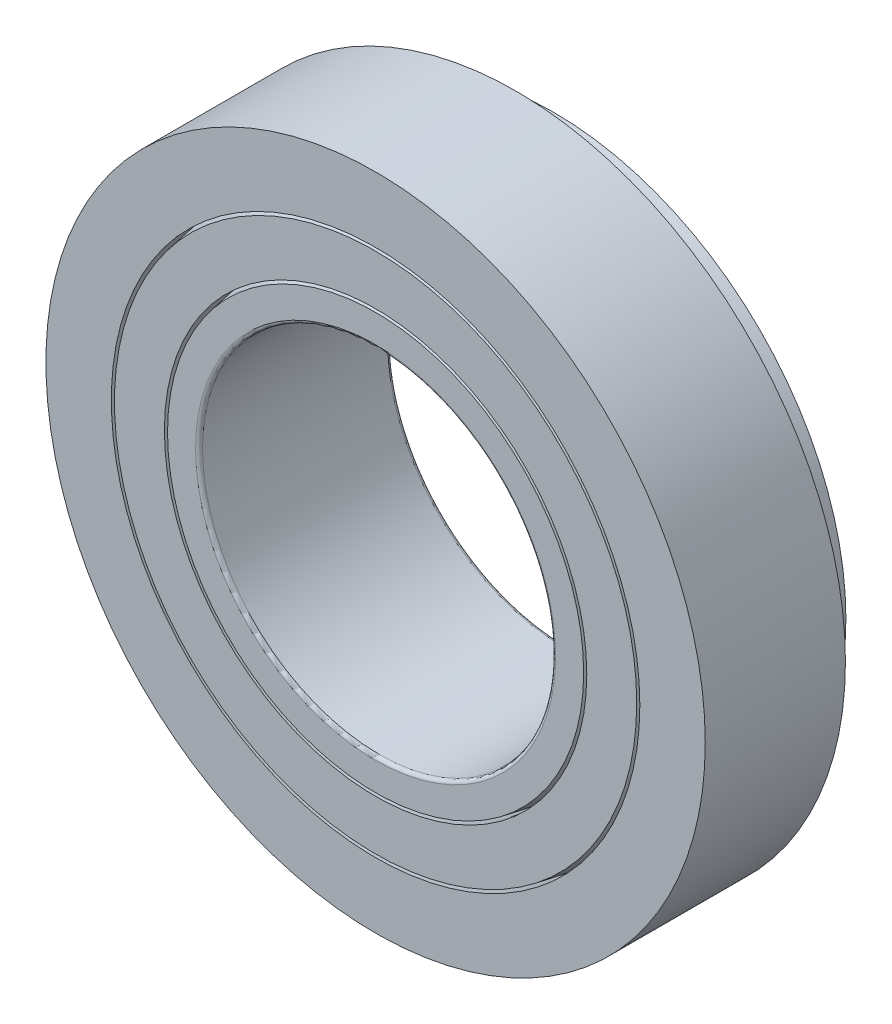
SolidWorks part; units mm, degrees
material "Alloy Steel"
ref_plane "Front Plane" through (0, 0, 0) normal (0, 0, 1) x (1, 0, 0)
ref_plane "Top Plane" through (0, 0, 0) normal (0, 1, 0) x (1, 0, 0)
ref_plane "Right Plane" through (0, 0, 0) normal (1, 0, 0) x (0, 0, -1)
sketch "Sketch1" plane through (0, 0, 0) normal (1, 0, 0) x (0, 0, -1)
  line L0 (-7.3422, 0) -> (7.3422, 0) construction
  line L1 (0, 0) -> (0, 25.2016) construction
  line L2 (-7.3422, 13.4937) -> (7.3422, 13.4937) construction
  line L3 (7.3422, 13.4937) -> (7.3422, 18.4944) construction
  line L4 (7.3422, 18.4944) -> (-7.3422, 15.9051) construction
  line L5 (-7.3422, 15.9051) -> (-7.3422, 13.4937) construction
  line L7 (-7.3422, 25.2016) -> (3.3734, 25.2016)
  line L8 (3.3734, 25.2016) -> (3.3734, 22.0904)
  line L9 (3.3734, 22.0904) -> (-7.3422, 20.2009)
  line L10 (-7.3422, 20.2009) -> (-7.3422, 25.2016)
  line L11 (-7.3422, 20.2009) -> (-6.6076, 16.0347) construction
  line L12 (6.2107, 22.5907) -> (6.9453, 18.4244) construction
  line L14 (-7.3422, 15.9051) -> (-6.6076, 16.0347) construction
  line L15 (-7.3422, 15.9051) -> (6.9453, 18.4244) construction
  point P5 (0, 13.4937)
  dimension "D1" = 100
  dimension "Width" = 14.6844
  dimension "OD" = 50.4031
  dimension "Shaft Dia" = 26.9875
  dimension "D2" = 11.7078
  dimension "D3" = 5.0006
  dimension "Outer Wd" = 10.7156
  dimension "Bearing Wd" = 14.2875
revolve "Revolve1" add sketch "Sketch1" angle 360 about L0
sketch "Sketch5" plane through (0, 0, 0) normal (1, 0, 0) x (0, 0, -1)
  line L0 (7.3422, 18.4944) -> (-7.3422, 15.9051) construction
  line L1 (7.3422, 18.4944) -> (-7.3422, 15.9051)
  line L2 (-7.3422, 15.9051) -> (-7.3422, 13.4937)
  line L3 (-7.3422, 13.4937) -> (7.3422, 13.4937)
  line L4 (7.3422, 13.4937) -> (7.3422, 18.4944)
revolve "Revolve4" add sketch "Sketch5" angle 360 about L0
sketch "Sketch2" plane through (0, 0, 0) normal (1, 0, 0) x (0, 0, -1)
  line L0 (-7.3422, 19.9616) -> (-7.3422, 16.1444)
  line L1 (3.3734, 21.8511) -> (6.2516, 22.3586)
  line L2 (-7.3422, 16.1444) -> (3.3734, 18.0339)
  line L3 (6.2107, 22.5907) -> (6.9453, 18.4244) construction
  line L4 (3.3734, 18.0339) -> (3.3734, 21.8511) construction
  line L5 (3.3734, 21.8511) -> (-7.3422, 19.9616)
  line L6 (3.3734, 22.0904) -> (-7.3422, 20.2009) construction
  line L7 (7.3422, 18.4944) -> (-7.3422, 15.9051) construction
  line L8 (-7.3422, 20.2009) -> (3.3734, 22.0904) construction
  line L9 (-7.3422, 15.9051) -> (6.9453, 18.4244) construction
  line L10 (6.2516, 22.3586) -> (6.9044, 18.6565)
  line L11 (-7.3422, 20.2009) -> (-7.3422, 19.9616) construction
  line L12 (-7.3422, 16.1444) -> (-7.3422, 15.9051) construction
  line L13 (3.3734, 25.2016) -> (3.3734, 22.0904) construction
  line L14 (6.9044, 18.6565) -> (3.3734, 18.0339)
  dimension "D1" = 4.2306
  dimension "D2" = 3.7592
revolve "Revolve2" add sketch "Sketch2" angle 360 about L0
sketch "Sketch3" plane through (0, 0, 0) normal (1, 0, 0) x (0, 0, -1)
  line L0 (-7.3422, 18.053) -> (3.3734, 19.9425) construction
  line L1 (-7.3422, 19.9616) -> (-7.3422, 16.1444) construction
  line L2 (3.3734, 18.0339) -> (3.3734, 21.8511) construction
  line L3 (-6.2402, 18.2473) -> (-6.6076, 20.3305)
  line L5 (-6.6076, 20.3305) -> (3.0061, 22.0256)
  line L6 (3.0061, 22.0256) -> (3.3734, 19.9425)
  line L7 (3.3734, 19.9425) -> (-6.2402, 18.2473)
  line L8 (3.3734, 22.0904) -> (-7.3422, 20.2009) construction
  line L9 (-7.3422, 18.053) -> (-6.9749, 18.1178) construction
  line L10 (-7.3422, 20.2009) -> (-6.6076, 16.0347) construction
  line L11 (-6.9749, 18.1178) -> (-6.6076, 18.1826) construction
  line L12 (-6.6076, 18.1826) -> (-6.2402, 18.2473) construction
revolve "Cut-Revolve1" cut sketch "Sketch3" angle 360 about L0
sketch "Sketch4" plane through (0, 0, 0) normal (1, 0, 0) x (0, 0, -1)
  line L0 (-6.5635, 20.0803) -> (3.0502, 21.7755)
  line L1 (3.0502, 21.7755) -> (3.3734, 19.9425)
  line L2 (3.3734, 19.9425) -> (-6.2402, 18.2473)
  line L3 (-7.3422, 18.053) -> (-6.2402, 18.2473) construction
  line L4 (-6.2402, 18.2473) -> (-6.5635, 20.0803)
  line L6 (3.3734, 19.9425) -> (-6.2402, 18.2473) construction
  line L7 (3.3734, 22.0904) -> (-7.3422, 20.2009) construction
  dimension "D1" = 0.254
revolve "Revolve3" add sketch "Sketch4" angle 360 about L0
ref_axis "Axis1" through (0, 0, -7.3422) along (0, 0, 1)
pattern_circular "CirPattern1" count 10 every 36 about axis through (0, 0, 0) along (0, 0, 1) of "Cut-Revolve1"
pattern_circular "CirPattern2" count 10 every 36 about axis through (0, 0, -7.3422) along (0, 0, 1) of bodies 403
fillet "Fillet1" [suppressed] radius 0.2679
fillet "Fillet2" radius 0.2679 2 edges at (13.4937, 0, -7.3422) (13.4937, 0, 7.3422)
sketch "Sketch6" [suppressed] plane through (0, 0, 0) normal (1, 0, 0) x (0, 0, -1)
  line L0 (-49.8078, 25.2016) -> (-49.8078, 20.2009)
  line L1 (-49.8078, 20.2009) -> (-39.0922, 22.0904)
  line L2 (-39.0922, 22.0904) -> (-39.0922, 25.2016)
  line L3 (-39.0922, 25.2016) -> (-49.8078, 25.2016)
  line L4 (-7.3422, 25.2016) -> (3.3734, 25.2016) construction
  line L5 (-7.3422, 20.2009) -> (-7.3422, 25.2016) construction
  line L6 (3.3734, 25.2016) -> (3.3734, 22.0904) construction
  line L8 (-7.3422, 24.9337) -> (-7.3422, -24.9337) construction
  dimension "D1" = 31.75
revolve "Revolve5" [suppressed] add sketch "Sketch6" angle 360 about L0
fillet "Fillet3" [suppressed] radius 0.2679
delete or keep bodies "Body-Delete1" [suppressed] type delete bodies bodies 399
equation "\"D3@Sketch1\" = \"D2@Sketch1\"/2.5"
equation "\"D2@Sketch2\" = \"D1@Sketch2\"*.75"
equation "\"Rollers@CirPattern2\" = \"OD@Sketch1\"*5"
equation "\"Angle@CirPattern2\" = 360/\"Rollers@CirPattern2\""
equation "\"D1@CirPattern1\" = \"Rollers@CirPattern2\""
equation "\"D2@CirPattern1\" = \"Angle@CirPattern2\""
equation "\"D1@Fillet1\" = \"Outer Wd@Sketch1\"*.025"
equation "\"D1@Fillet2\" = \"D1@Fillet1\""
equation "\"D1@Fillet3\" = \"D1@Fillet1\""
